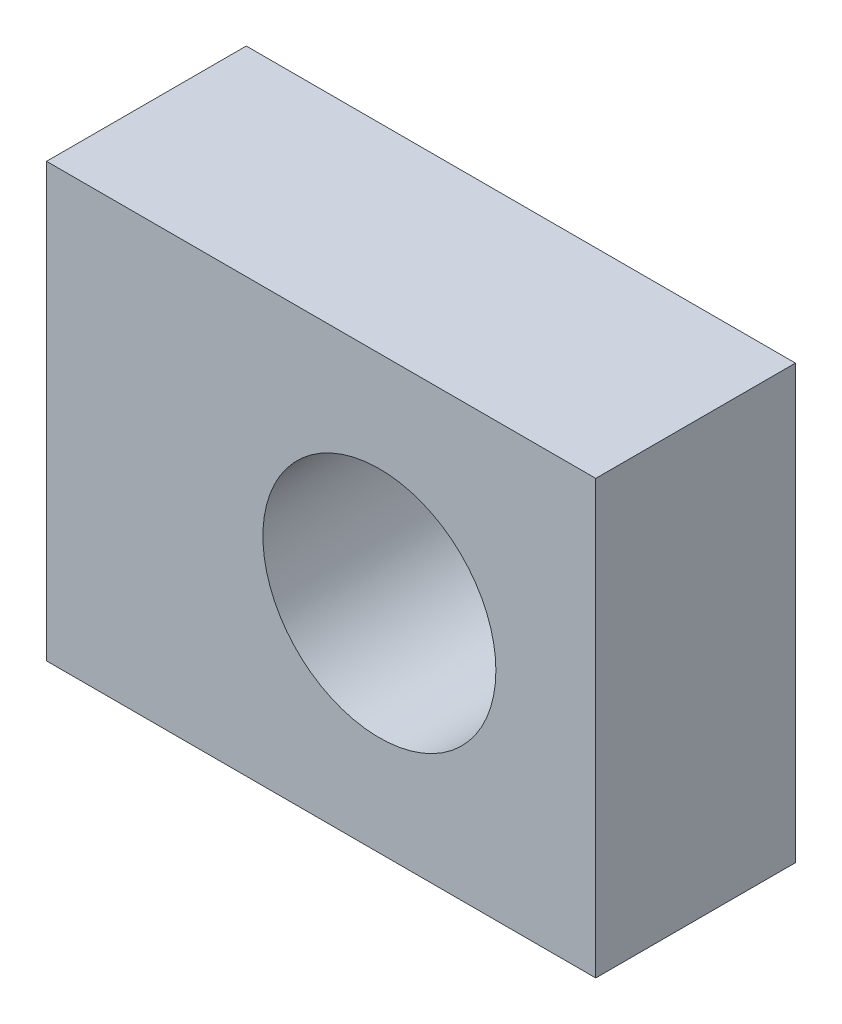
SolidWorks part; units mm, degrees
ref_plane "Plan de face" through (0, 0, 0) normal (0, 0, 1) x (1, 0, 0)
ref_plane "Plan de dessus" through (0, 0, 0) normal (0, 1, 0) x (1, 0, 0)
ref_plane "Plan de droite" through (0, 0, 0) normal (1, 0, 0) x (0, 0, -1)
sketch "Esquisse1" plane through (0, 0, 0) normal (0, 0, 1) x (1, 0, 0)
  line L1 (-16.5, 13) -> (16.5, 13)
  line L2 (-16.5, 13) -> (-16.5, -13)
  line L3 (-16.5, -13) -> (16.5, -13)
  line L4 (16.5, 13) -> (16.5, -13)
  line L5 (-16.5, 13) -> (16.5, -13) construction
  line L6 (-16.5, -13) -> (16.5, 13) construction
  point P0 (0, 0)
  dimension "D1" = 33
  dimension "D2" = 26
extrude "Boss.-Extru.1" add sketch "Esquisse1" along normal blind 12
sketch "Esquisse2" plane through (0, 0, 12) normal (0, 0, 1) x (1, 0, 0)
  circle A0 centre (3.5, 0) radius 7
extrude "Enlèv. mat.-Extru.1" cut sketch "Esquisse2" against normal through all contours A0
